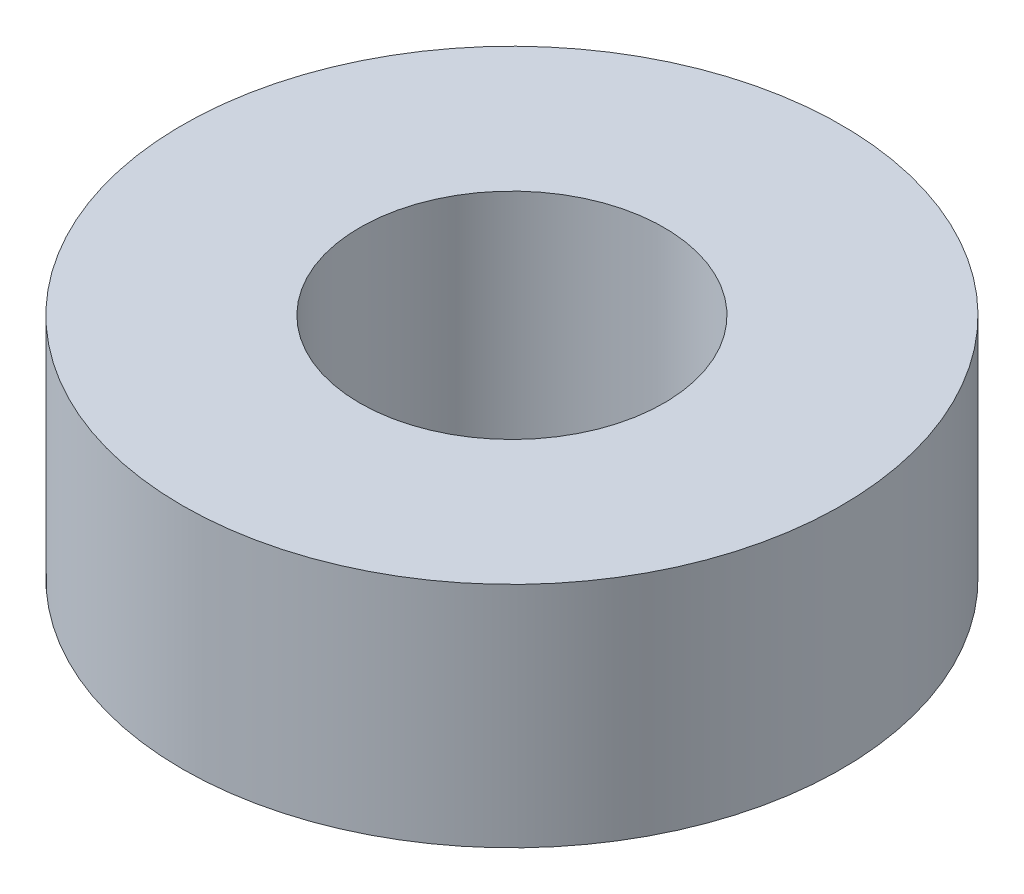
SolidWorks part; units mm, degrees
ref_plane "Front Plane" through (0, 0, 0) normal (0, 0, 1) x (1, 0, 0)
ref_plane "Top Plane" through (0, 0, 0) normal (0, 1, 0) x (1, 0, 0)
ref_plane "Right Plane" through (0, 0, 0) normal (1, 0, 0) x (0, 0, -1)
sketch "Sketch1" plane through (0, 0, 0) normal (0, 1, 0) x (1, 0, 0)
  circle A0 centre (0, 0) radius 6.5
  circle A1 centre (0, 0) radius 3
  dimension "D1" = 13
  dimension "D2" = 6
extrude "Boss-Extrude2" add sketch "Sketch1" along normal blind 4.5
